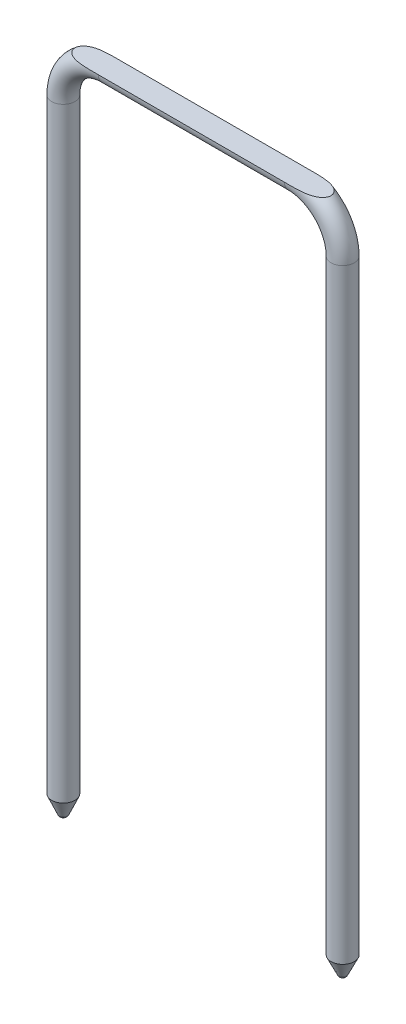
SolidWorks part; units mm, degrees
ref_plane "Front Plane" through (0, 0, 0) normal (0, 0, 1) x (1, 0, 0)
ref_plane "Top Plane" through (0, 0, 0) normal (0, 1, 0) x (1, 0, 0)
ref_plane "Right Plane" through (0, 0, 0) normal (1, 0, 0) x (0, 0, -1)
sketch "Sketch3" plane through (0, 0, 0) normal (0, 1, 0) x (1, 0, 0)
  circle A0 centre (0, 0) radius 2.5
sketch "Sketch4" plane through (0, 0, 0) normal (0, 0, 1) x (1, 0, 0)
  line L0 (0, 0) -> (0, 130)
  line L1 (60, 130) -> (60, 24.6009)
  line L2 (60, 24.6009) -> (60, 0)
  line L4 (10, 140) -> (50, 140)
  arc A0 (0, 130) -> (10, 140) centre (10, 130) cw
  arc A1 (50, 140) -> (60, 130) centre (50, 130) cw
  dimension "D1" = 10
  dimension "D2" = 130
sweep "Sweep1" add profiles "Sketch3" path "Sketch4"
sketch "Sketch5" plane through (0, 0, 0) normal (0, 0, 1) x (1, 0, 0)
  line L0 (0, 0) -> (0, -4.2)
  line L1 (0, 0) -> (2.5, 0)
  line L2 (2.5, 0) -> (0.9219, -3.6418)
  spline S0 degree 2 poles (0.9219, -3.6418) (0.6292, -4.3279) (0, -4.2) knots 0 0 0 1 1 1
revolve "Revolve1" add sketch "Sketch5" angle 360 about L0
sketch "Sketch6" plane through (0, 0, 0) normal (0, 0, 1) x (1, 0, 0)
  line L0 (57.5, 0) -> (62.5, 0) construction
  line L1 (57.5, 0) -> (60, 0)
  line L2 (60, 0) -> (60, -4)
  line L3 (57.5, 0) -> (59.1238, -3.438)
  spline S0 degree 2 poles (59.1238, -3.438) (59.3757, -4.1374) (60, -4) knots 0 0 0 1 1 1
revolve "Revolve2" add sketch "Sketch6" angle 360 about L2
ref_plane "Plane2" through (0, 10, 0) normal (0, 1, 0) x (1, 0, 0)
sketch "Sketch7" plane through (0, 0, 0) normal (1, 0, 0) x (0, 0, -1)
  line L0 (-3.4024, 140) -> (3.1154, 140)
  line L1 (3.1154, 140) -> (3.1154, 144.3221)
  line L2 (3.1154, 144.3221) -> (-3.4024, 144.3221)
  line L3 (-3.4024, 144.3221) -> (-3.4024, 140)
  circle A0 centre (0, 140) radius 2.5 construction
extrude "Cut-Extrude1" cut sketch "Sketch7" along normal blind 72
